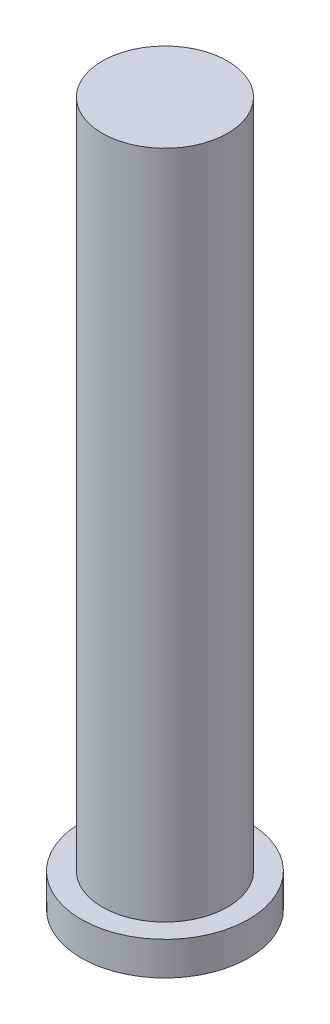
SolidWorks part; units mm, degrees
ref_plane "Front Plane" through (0, 0, 0) normal (0, 0, 1) x (1, 0, 0)
ref_plane "Top Plane" through (0, 0, 0) normal (0, 1, 0) x (1, 0, 0)
ref_plane "Right Plane" through (0, 0, 0) normal (1, 0, 0) x (0, 0, -1)
sketch "Sketch1" plane through (0, 0, 0) normal (0, 1, 0) x (1, 0, 0)
  circle A0 centre (0, 0) radius 6.35
  dimension "D1" = 12.7
extrude "Boss-Extrude1" add sketch "Sketch1" along normal blind 2.54
sketch "Sketch2" plane through (0, 2.54, 0) normal (0, 1, 0) x (1, 0, 0)
  circle A0 centre (0, 0) radius 4.7498
  dimension "D1" = 9.4996
extrude "Boss-Extrude2" add sketch "Sketch2" along normal blind 50.8
